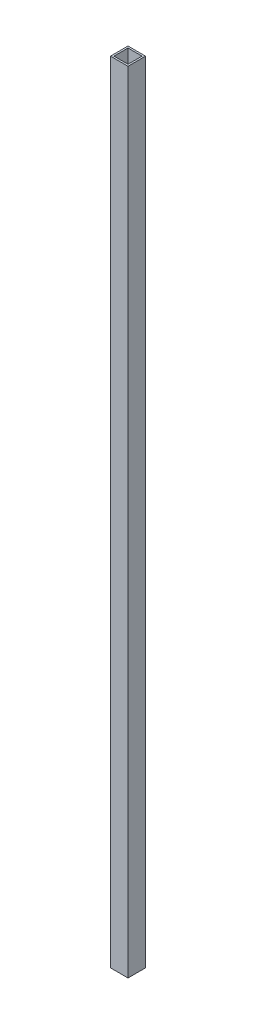
SolidWorks part; units mm, degrees
material "Custom Plastic"
ref_plane "Front Plane" through (0, 0, 0) normal (0, 0, 1) x (1, 0, 0)
ref_plane "Top Plane" through (0, 0, 0) normal (0, 1, 0) x (1, 0, 0)
ref_plane "Right Plane" through (0, 0, 0) normal (1, 0, 0) x (0, 0, -1)
sketch "Sketch1" plane through (0, 0, 0) normal (0, 0, 1) x (1, 0, 0)
  line L1 (-31.7391, 49.7826) -> (-11.7391, 49.7826)
  line L2 (-31.7391, 49.7826) -> (-31.7391, -850.2174)
  line L3 (-31.7391, -850.2174) -> (-11.7391, -850.2174)
  line L4 (-11.7391, 49.7826) -> (-11.7391, -850.2174)
  dimension "D1" = 20
  dimension "D2" = 900
extrude "Boss-Extrude1" add sketch "Sketch1" against normal blind 20
sketch "Sketch2" plane through (0, 49.7826, 0) normal (0, 1, 0) x (1, 0, 0)
  line L8 (-29.7391, 2) -> (-13.7391, 2)
  line L9 (-13.7391, 2) -> (-13.7391, 18)
  line L10 (-13.7391, 18) -> (-29.7391, 18)
  line L11 (-29.7391, 18) -> (-29.7391, 2)
  line L12 (-29.7391, 2) -> (-13.7391, 2)
  line L13 (-13.7391, 2) -> (-13.7391, 18)
  line L14 (-13.7391, 18) -> (-29.7391, 18)
  line L15 (-29.7391, 18) -> (-29.7391, 2)
  dimension "D1" = 2
extrude "Cut-Extrude1" cut sketch "Sketch2" against normal blind 200
